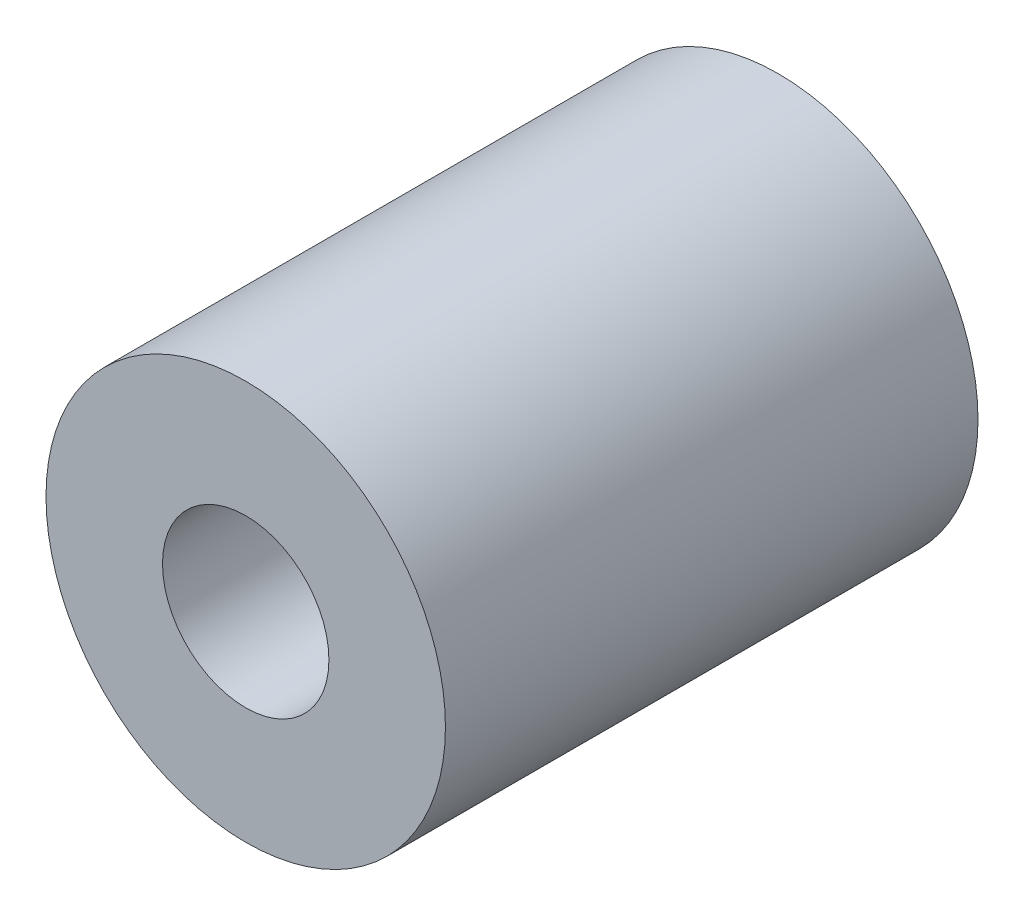
SolidWorks part; units mm, degrees
ref_plane "Front Plane" through (0, 0, 0) normal (0, 0, 1) x (1, 0, 0)
ref_plane "Top Plane" through (0, 0, 0) normal (0, 1, 0) x (1, 0, 0)
ref_plane "Right Plane" through (0, 0, 0) normal (1, 0, 0) x (0, 0, -1)
sketch "Sketch1" plane through (0, 0, 0) normal (0, 0, 1) x (1, 0, 0)
  line L0 (0, 0) -> (50000, 0) construction
  line L1 (0, 0) -> (0, -50000) construction
  circle A0 centre (0, 0) radius 19.05
  dimension "D1" = 38.1
extrude "Boss-Extrude1" add sketch "Sketch1" against normal blind 50.8
sketch "Sketch2" plane through (0, 0, 0) normal (0, 0, 1) x (1, 0, 0)
  circle A0 centre (0, 0) radius 7.9375
  dimension "D1" = 15.875
extrude "Cut-Extrude1" cut sketch "Sketch2" against normal blind 63.5
